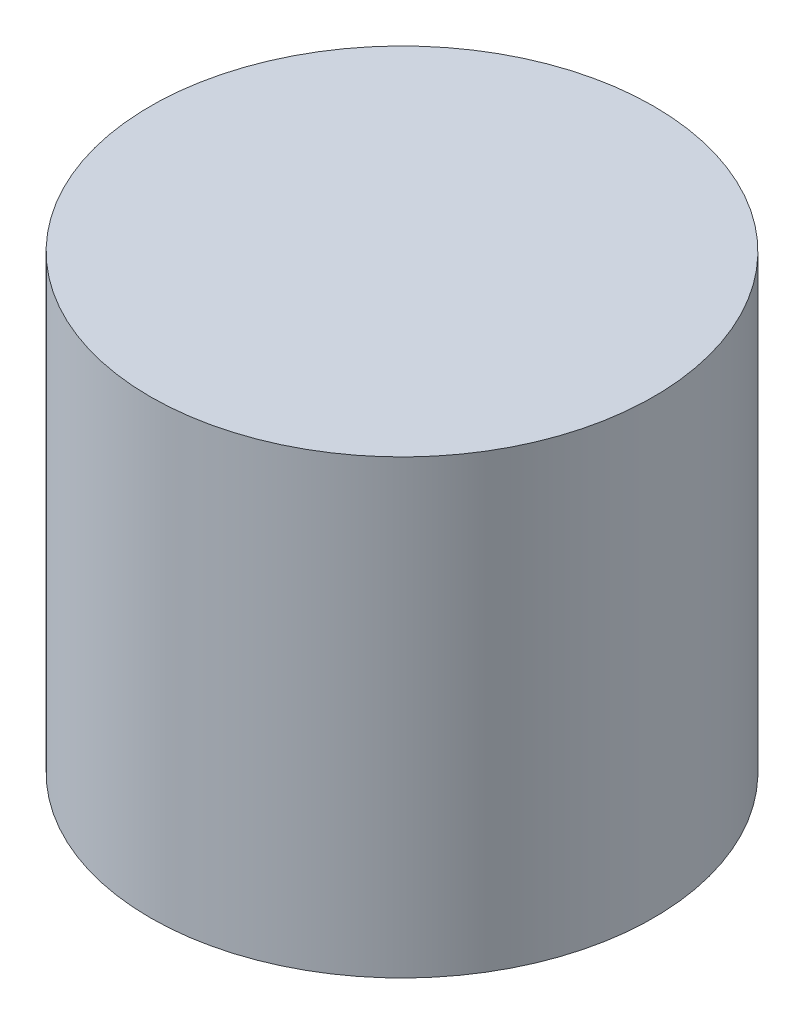
SolidWorks part; units mm, degrees
ref_plane "Front Plane" through (0, 0, 0) normal (0, 0, 1) x (1, 0, 0)
ref_plane "Top Plane" through (0, 0, 0) normal (0, 1, 0) x (1, 0, 0)
ref_plane "Right Plane" through (0, 0, 0) normal (1, 0, 0) x (0, 0, -1)
sketch "Sketch1" plane through (0, 0, 0) normal (0, 1, 0) x (1, 0, 0)
  circle A0 centre (0, 0) radius 7.25
  dimension "D1" = 14.5
extrude "Boss-Extrude1" add sketch "Sketch1" along normal blind 13
sketch "Sketch2" plane through (0, 0, 0) normal (0, -1, 0) x (-1, 0, 0)
  circle A0 centre (0, 0) radius 5.25
  dimension "D1" = 10.5
extrude "Cut-Extrude1" cut sketch "Sketch2" against normal blind 11 contours A0
